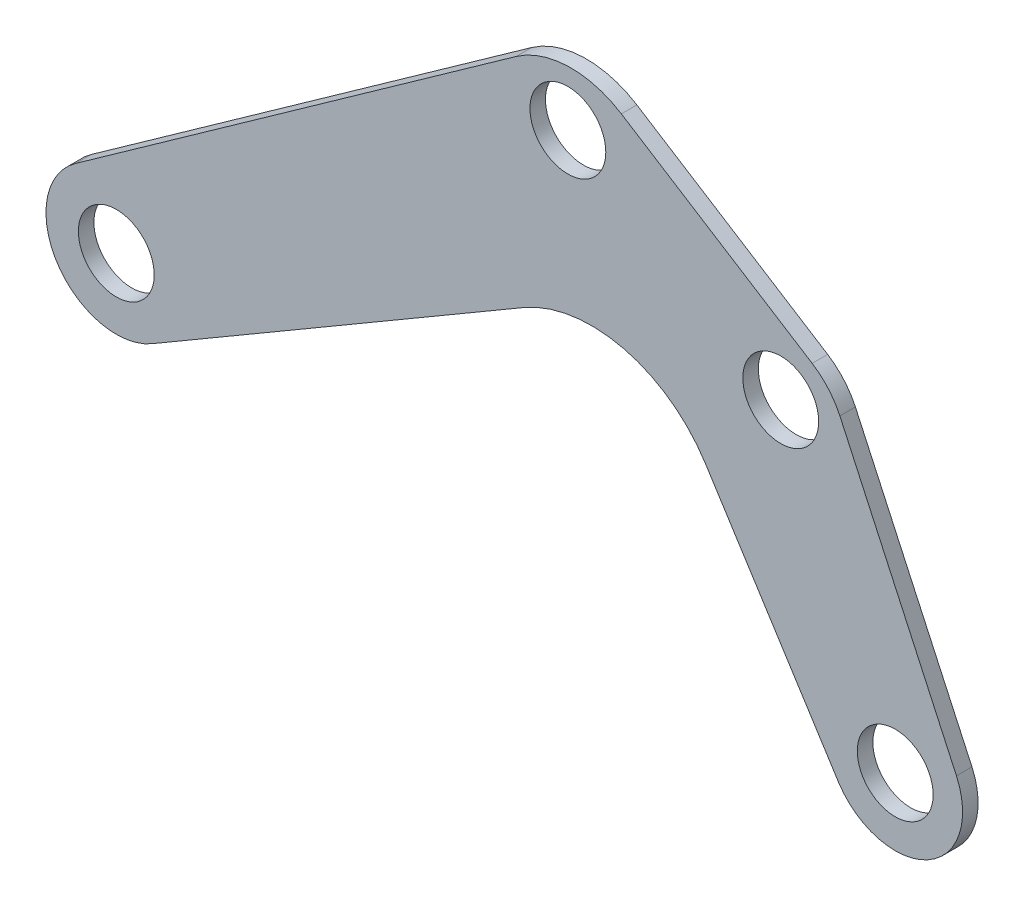
SolidWorks part; units mm, degrees
ref_plane "Front Plane" through (0, 0, 0) normal (0, 0, 1) x (1, 0, 0)
ref_plane "Top Plane" through (0, 0, 0) normal (0, 1, 0) x (1, 0, 0)
ref_plane "Right Plane" through (0, 0, 0) normal (1, 0, 0) x (0, 0, -1)
ref_plane "Plane1" through (0, 0, 0) normal (0, 0, -1) x (-1, 0, 0)
sketch "Sketch1" plane through (0, 0, 0) normal (0, 0, -1) x (-1, 0, 0)
  line L3 (316.4386, 42.9491) -> (130.9909, 174.6712)
  line L4 (130.9909, 174.6712) -> (31.9811, 112.057)
  line L23 (105.4341, 104.9996) -> (287.7291, -1.5037)
  line L25 (31.9811, 112.057) -> (-15.3782, 9.1007)
  line L29 (105.4341, 104.9996) -> (28.9483, -15.337)
  circle A0 centre (301.0897, 21.3648) radius 14.2875
  circle A1 centre (130.9909, 146.5103) radius 14.2875
  arc A2 (287.7291, -1.5037) -> (316.4386, 42.9491) centre (301.0897, 21.3648) ccw
  arc A4 (-15.3782, 9.1007) -> (28.9483, -15.337) centre (7.6751, -1.5037) ccw
  circle A10 centre (50.8, 98.679) radius 14.2875
  circle A11 centre (7.6751, -1.5037) radius 14.2875
  point P7 (94.3377, 98.679)
  point P8 (107.4629, 102.2507)
  point P10 (7.6751, 0)
  point P11 (99.1481, 98.679)
  point P12 (105.4341, 104.9996)
  point P13 (103.8098, 104.9996)
  point P14 (31.9811, 112.057)
  dimension "D1" = 28.575
  dimension "D2" = 28.575
extrude "Boss-Extrude1" add sketch "Sketch1" against normal blind 5.842
fillet "Fillet6" radius 35.56 1 edges at (-130.9909, 174.6712, 2.921)
fillet "Fillet10" radius 27.94 1 edges at (-31.9811, 112.057, 2.921)
fillet "Fillet13" radius 50.8 1 edges at (-105.4341, 104.9996, 2.921)
